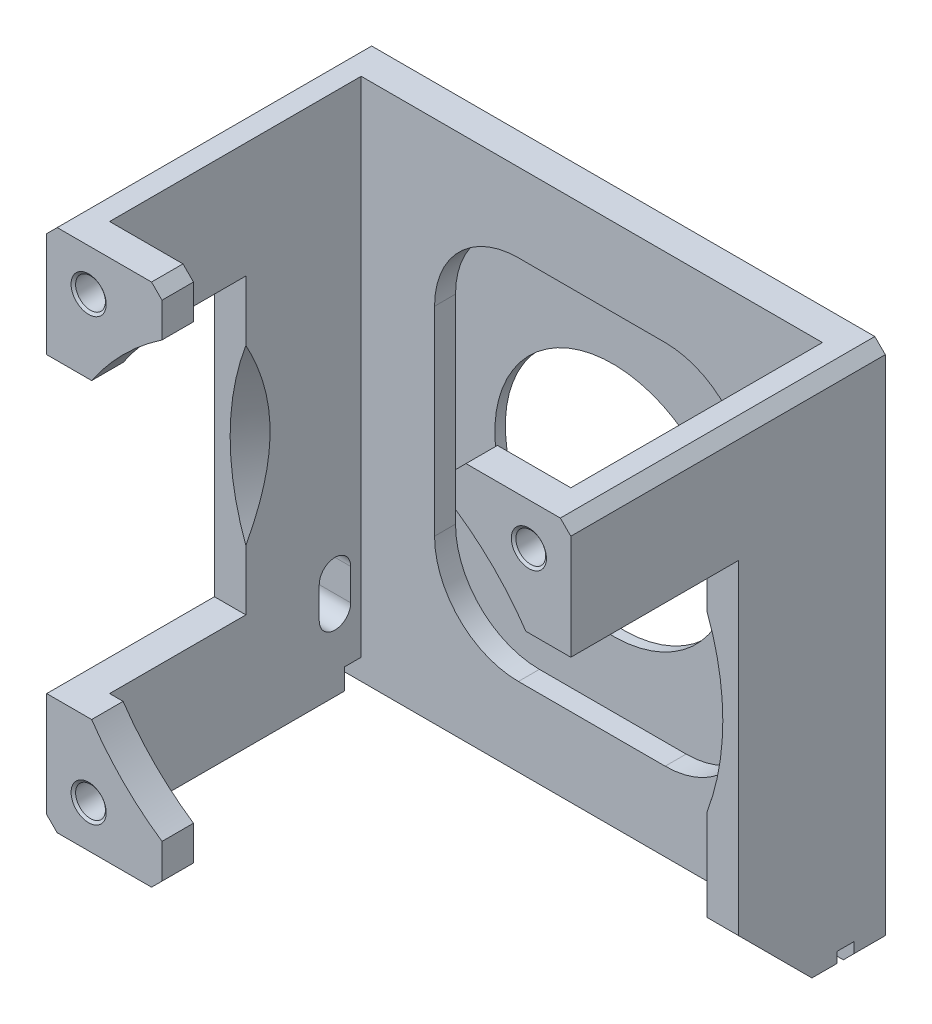
SolidWorks part; units mm, degrees
material "6063-T1"
ref_plane "Спереди" through (0, 0, 0) normal (0, 0, 1) x (1, 0, 0)
ref_plane "Сверху" through (0, 0, 0) normal (0, 1, 0) x (1, 0, 0)
ref_plane "Справа" through (0, 0, 0) normal (1, 0, 0) x (0, 0, -1)
sketch "Эскиз1" plane through (0, 0, 0) normal (0, 1, 0) x (1, 0, 0)
  line L0 (-22, -12) -> (-22, 12)
  line L1 (-25, -15) -> (25, -15)
  line L2 (-25, -15) -> (-25, 15)
  line L3 (-25, 15) -> (25, 15)
  line L4 (25, -15) -> (25, 15)
  line L5 (-25, -15) -> (25, 15) construction
  line L6 (-25, 15) -> (25, -15) construction
  line L7 (-22, 12) -> (22, 12)
  line L8 (22, -12) -> (22, 12)
  line L9 (-22, -12) -> (22, -12)
  point P0 (0, 0)
  dimension "D1" = 50
  dimension "D2" = 30
  dimension "D3" = 3
extrude "Бобышка-Вытянуть1" add sketch "Эскиз1" along normal blind 50
sketch "Эскиз2" plane through (0, 0, -15) normal (0, 0, -1) x (-1, 0, 0)
  line L1 (-20.7123, 39) -> (-25, 39)
  line L2 (-25, 50) -> (-25, 0) construction
  line L3 (-20.7123, 11) -> (-25, 11)
  line L4 (-14, 4.2877) -> (-14, 0)
  line L5 (-25, 0) -> (25, 0) construction
  line L6 (14, 4.2877) -> (14, 0)
  line L7 (20.7123, 11) -> (25, 11)
  line L8 (25, 50) -> (25, 0) construction
  line L9 (20.7123, 39) -> (25, 39)
  line L10 (14, 45.7123) -> (14, 50)
  line L11 (-25, 50) -> (25, 50) construction
  line L12 (-14, 45.7123) -> (-14, 50)
  arc A2 (14, 4.2877) -> (20.7123, 11) centre (0, 25) ccw
  arc A4 (20.7123, 39) -> (14, 45.7123) centre (0, 25) ccw
  arc A6 (-14, 45.7123) -> (-20.7123, 39) centre (0, 25) ccw
  arc A8 (-20.7123, 11) -> (-14, 4.2877) centre (0, 25) ccw
  line M9 (-25, 0) -> (25, 0)
  line M10 (25, 0) -> (25, 50)
  line M11 (25, 50) -> (-25, 50)
  line M12 (-25, 50) -> (-25, 0)
  dimension "D1" = 25
  dimension "D2" = 25
  dimension "D5" = 25
  dimension "D3" = 28
  dimension "D4" = 28
extrude "Вырез-Вытянуть1" cut sketch "Эскиз2" against normal through all from offset 14 contours L3 A8 L4 L6 A2 L7 L9 A4 L10 L12 A6 L1 M9 M10 M11 M12 | A8 L3 L4 M12 M9
sketch "Эскиз3" plane through (0, 0, -12) normal (0, 0, 1) x (1, 0, 0)
  circle A0 centre (0, 25) radius 11.25
  dimension "D1" = 22.5
extrude "Вырез-Вытянуть2" cut sketch "Эскиз3" against normal through all
ref_axis "Ось1" through (0, 25, -15) along (0, 0, 1)
ref_plane "Плоскость1" through (0, 25, 0) normal (0, 1, 0) x (-1, 0, 0)
sketch "Эскиз6" plane through (0, 25, 0) normal (0, 1, 0) x (-1, 0, 0)
  line L0 (-23.5, -1) -> (-22, -3.3098)
  line L1 (-22, -3.3098) -> (-22, -1)
  line L2 (-22, -1) -> (-23.5, -1)
  line L3 (0, -15) -> (0, -12) construction
  line L5 (-22, 12) -> (-22, -12) construction
  dimension "D1" = 33
  dimension "D2" = 1.5
revolve "Вырез-Повернуть1" cut sketch "Эскиз6" angle 360 about axis through (0, 25, -15) along (0, 0, 1)
hole_wizard "Отверстие #4-40" positions "Эскиз8" profile "Эскиз7" tap size "#4-40" standard "Ansi (в дюймах)" end condition up to next
sketch "Эскиз8" plane through (0, 0, 15) normal (0, 0, 1) x (1, 0, 0)
  circle A3 centre (0, 25) radius 11.25 construction
  point P1 (-21, 46)
  point P4 (21, 46)
  point P7 (-21, 4)
  dimension "D4" = 21
  dimension "D1" = 42
  dimension "D2" = 42
  dimension "D3" = 21
sketch "Эскиз7" plane through (-21, 46, 15) normal (1, 0, 0) x (0, -1, 0)
  line L0 (0, 0) -> (0, 3)
  line L1 (0, 3) -> (1.4224, 3)
  line L2 (1.4224, 3) -> (1.4224, 0.1779)
  line L3 (1.4224, 0.1779) -> (1.6764, 0)
  line L5 (1.6764, 0) -> (0, 0)
  line L6 (-1.4224, 0.1779) -> (-1.6764, 0) construction
  line L11 (0, -6.35) -> (0, 107.95) construction
  dimension "Диаметр резьбы" = 2.8448
  dimension "Глубина проходного сверла" = 3
  dimension "Диаметр передней зенковки" = 3.3528
  dimension "Угол передней зенковки" = 110
sketch "Эскиз10" plane through (-25, 0, 0) normal (-1, 0, 0) x (0, 0, 1)
  line L0 (-12, 0) -> (-12, 2)
  line L1 (-15, 50) -> (-15, 0) construction
  line L2 (-12, 2) -> (-10.4, 2)
  line L3 (-10.4, 2) -> (-10.4, 0)
  line L4 (-12, 0) -> (-10.4, 0)
  line L5 (-15, 0) -> (15, 0) construction
  dimension "D1" = 1.6
  dimension "D2" = 2
  dimension "D3" = 3
extrude "Вырез-Вытянуть4" cut sketch "Эскиз10" against normal through all
sketch "Эскиз9" plane through (0, 0, -12) normal (0, 0, 1) x (1, 0, 0)
  line L7 (-7, 7.5) -> (7, 7.5)
  line L8 (-15, 15.5) -> (-15, 34.5)
  line L9 (-7, 42.5) -> (7, 42.5)
  line L10 (15, 15.5) -> (15, 34.5)
  line L11 (-15, 7.5) -> (15, 42.5) construction
  line L12 (-15, 42.5) -> (15, 7.5) construction
  arc A0 (-15, 15.5) -> (-7, 7.5) centre (-7, 15.5) ccw
  arc A1 (7, 7.5) -> (15, 15.5) centre (7, 15.5) ccw
  arc A2 (15, 34.5) -> (7, 42.5) centre (7, 34.5) ccw
  arc A3 (-7, 42.5) -> (-15, 34.5) centre (-7, 34.5) ccw
  circle A5 centre (0, 25) radius 11.25 construction
  point P19 (0, 25)
  dimension "D1" = 8
  dimension "D2" = 35
  dimension "D3" = 30
extrude "Вырез-Вытянуть3" cut sketch "Эскиз9" against normal blind 2
chamfer "Фаска1" distance 8 angle 45 1 edges at (23.5, 0, -1)
chamfer "Фаска2" distance 1 angle 45 9 edges at (25, 0, -9.7) (25, 0, -13.5) (-25, 0, 2.3) (-25, 0, -13.5) (-14, 0, 13.5) (-25, 50, 0) (25, 50, 0) (-14, 50, 13.5) (14, 50, 13.5)
sketch "Эскиз11" plane through (-25, 0, 0) normal (-1, 0, 0) x (0, 0, 1)
  line L0 (-9.5, 10) -> (-9.5, 7) construction
  line L1 (-8, 10) -> (-8, 7)
  line L2 (-11, 10) -> (-11, 7)
  line L4 (-15, 49) -> (-15, 1) construction
  line L5 (-12, 0) -> (-15, 0) construction
  arc A0 (-8, 10) -> (-11, 10) centre (-9.5, 10) ccw
  arc A1 (-11, 7) -> (-8, 7) centre (-9.5, 7) ccw
  point P2 (-9.5, 8.5)
  dimension "D1" = 3
  dimension "D2" = 6
  dimension "D3" = 5.5
  dimension "D4" = 8.5
extrude "Вырез-Вытянуть5" cut sketch "Эскиз11" against normal up to next
